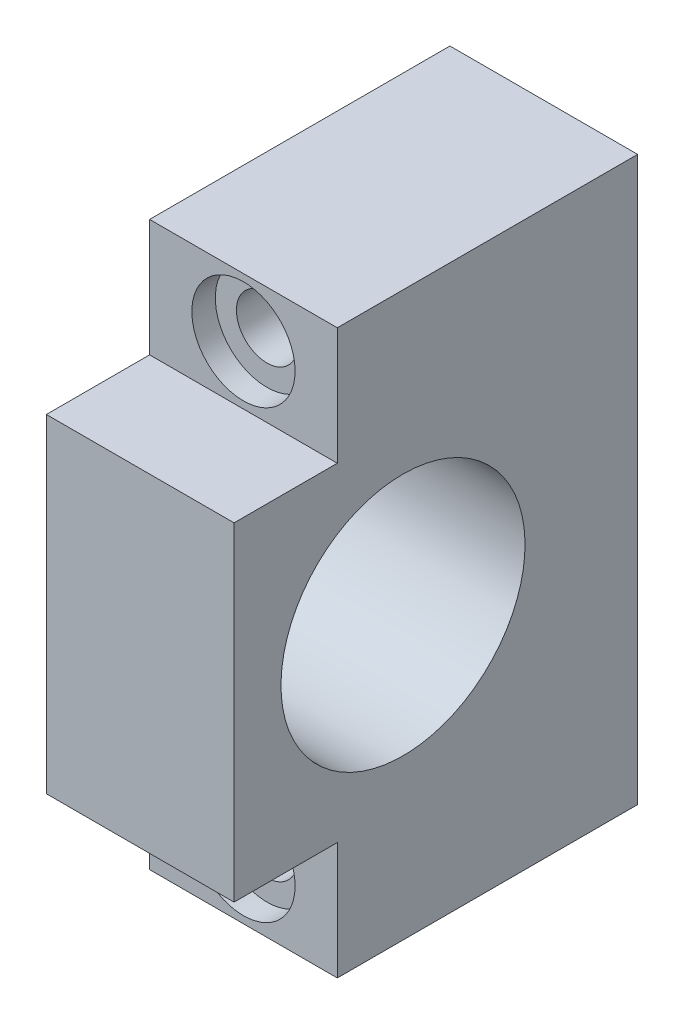
SolidWorks part; units mm, degrees
material "1.0037 (S235JR)"
ref_plane "Front Plane" through (0, 0, 0) normal (0, 0, 1) x (1, 0, 0)
ref_plane "Top Plane" through (0, 0, 0) normal (0, 1, 0) x (1, 0, 0)
ref_plane "Right Plane" through (0, 0, 0) normal (1, 0, 0) x (0, 0, -1)
sketch "Sketch1" plane through (0, 0, 0) normal (0, 0, 1) x (1, 0, 0)
  line L1 (-10, 30) -> (10, 30)
  line L2 (-10, 30) -> (-10, -30)
  line L3 (-10, -30) -> (10, -30)
  line L4 (10, 30) -> (10, -30)
  line L5 (-10, 30) -> (10, -30) construction
  line L6 (-10, -30) -> (10, 30) construction
  point P0 (0, 0)
  dimension "D1" = 20
  dimension "D2" = 60
extrude "Boss-Extrude1" add sketch "Sketch1" along normal blind 43
sketch "Sketch2" plane through (0, 0, 43) normal (0, 0, 1) x (1, 0, 0)
  line L0 (10, -30) -> (10, 30) construction
  line L1 (-10, -30) -> (10, -30)
  line L2 (-10, -30) -> (-10, -17.5)
  line L3 (-10, -17.5) -> (10, -17.5)
  line L4 (10, -30) -> (10, -17.5)
  line L6 (-10, 30) -> (10, 30)
  line L7 (-10, 30) -> (-10, 17.5)
  line L8 (-10, 17.5) -> (10, 17.5)
  line L9 (10, 30) -> (10, 17.5)
  dimension "D1" = 12.5
  dimension "D2" = 12.5
extrude "Cut-Extrude1" cut sketch "Sketch2" against normal blind 11
sketch "Sketch3" plane through (0, 0, 32) normal (0, 0, 1) x (1, 0, 0)
  line L0 (-10, -30) -> (10, -30) construction
  line L1 (10, 30) -> (-10, 30) construction
  circle A0 centre (0, -23.75) radius 3.25
  circle A1 centre (0, 23.75) radius 3.25
  dimension "D1" = 6.5
  dimension "D2" = 6.5
  dimension "D3" = 6.25
  dimension "D4" = 6.25
extrude "Cut-Extrude2" cut sketch "Sketch3" against normal through all
sketch "Sketch4" plane through (0, 0, 32) normal (0, 0, 1) x (1, 0, 0)
  circle A0 centre (0, -23.75) radius 5.5
  circle A1 centre (0, 23.75) radius 5.5
  dimension "D1" = 11
  dimension "D2" = 11
extrude "Cut-Extrude3" cut sketch "Sketch4" against normal blind 2.5
sketch "Sketch5" plane through (10, 0, 0) normal (1, 0, 0) x (0, 0, -1)
  circle A0 centre (-25, 0) radius 13
  dimension "D1" = 26
  dimension "D2" = 25
extrude "Cut-Extrude4" cut sketch "Sketch5" against normal through all
